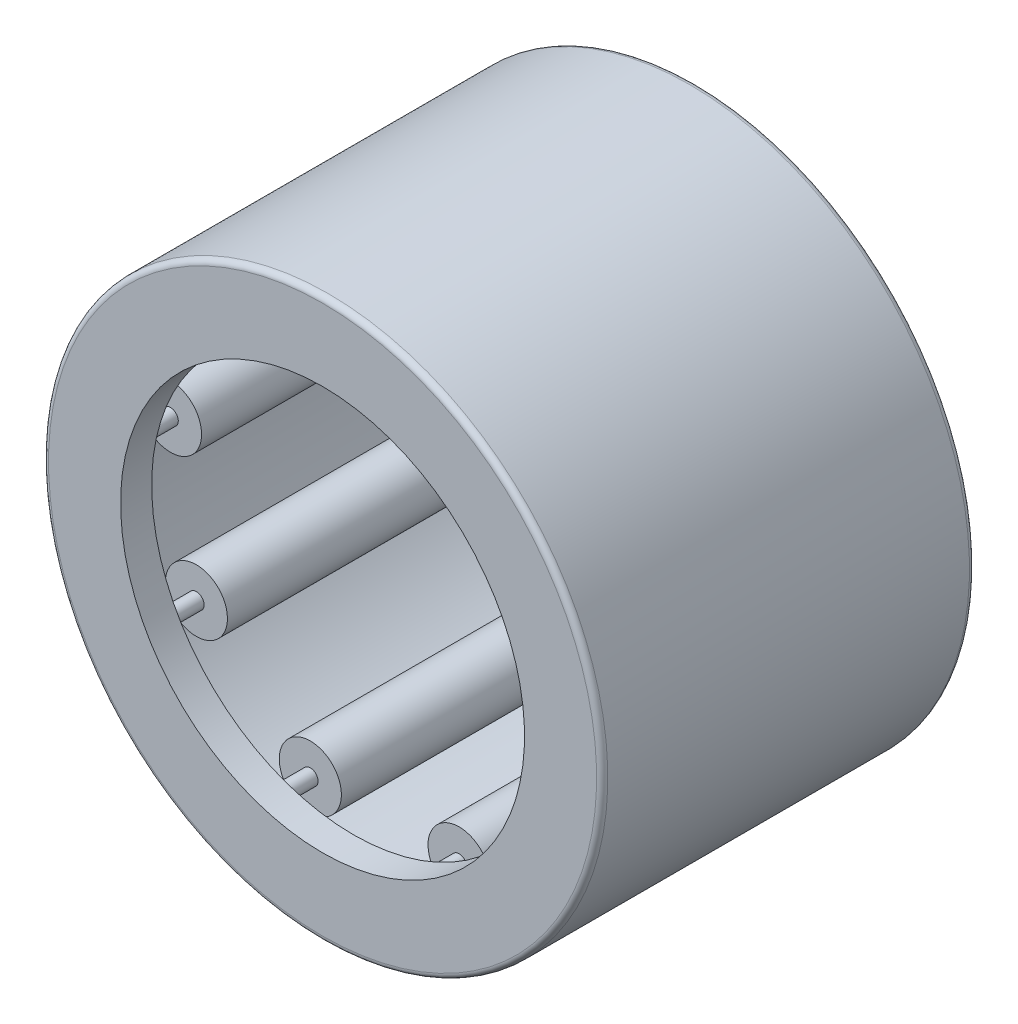
SolidWorks part; units mm, degrees
ref_plane "Front Plane" through (0, 0, 0) normal (0, 0, 1) x (1, 0, 0)
ref_plane "Top Plane" through (0, 0, 0) normal (0, 1, 0) x (1, 0, 0)
ref_plane "Right Plane" through (0, 0, 0) normal (1, 0, 0) x (0, 0, -1)
sketch "Sketch1" plane through (0, 0, 0) normal (1, 0, 0) x (0, 0, -1)
  line L0 (-4, 0) -> (4, 0) construction
  line L1 (0, 0) -> (0, 6) construction
  line L2 (-4, 0) -> (-4, 6) construction
  line L3 (-4, 6) -> (4, 6)
  line L4 (4, 6) -> (4, 0) construction
  line L5 (4, 0) -> (3.3333, 0) construction
  line L6 (3.3333, 0) -> (3.3333, 5.3333) construction
  line L7 (3.3333, 5.3333) -> (-3.3333, 5.3333)
  line L8 (-3.3333, 5.3333) -> (-3.3333, 0) construction
  line L9 (-3.3333, 0) -> (-4, 0) construction
  line L10 (-4, 6) -> (-4, 4.3333)
  line L11 (-4, 4.3333) -> (-3.3333, 4.3333)
  line L12 (-3.3333, 4.3333) -> (-3.3333, 5.3333)
  line L13 (3.3333, 6) -> (3.3333, 5.3333) construction
  line L14 (3.3333, 5.3333) -> (3.3333, 4.3333)
  line L15 (3.3333, 4.3333) -> (4, 4.3333)
  line L16 (4, 4.3333) -> (4, 6)
  line L17 (3.3333, 5.3333) -> (3.3333, 4.6667) construction
  line L18 (3.3333, 4.6667) -> (3.3333, 4) construction
  line L19 (3.3333, -5.3333) -> (3.3333, -4.6667) construction
  line L20 (3.3333, -6) -> (3.3333, -5.3333) construction
  line L21 (4, -4.3333) -> (4, -6) construction
  line L22 (3.3333, -4.3333) -> (4, -4.3333) construction
  line L23 (3.3333, -5.3333) -> (3.3333, -4.3333) construction
  line L24 (-3.3333, -4.3333) -> (-3.3333, -5.3333) construction
  line L25 (-4, -4.3333) -> (-3.3333, -4.3333) construction
  line L26 (-4, -6) -> (-4, -4.3333) construction
  line L27 (3.3333, -5.3333) -> (-3.3333, -5.3333) construction
  line L28 (-4, -6) -> (4, -6) construction
  point P5 (0, 4)
  dimension "Width" = 8
  dimension "OD" = 12
  dimension "Shaft Dia" = 8
revolve "Revolve1" add sketch "Sketch1" angle 360 about L0
sketch "Sketch2" plane through (0, 0, 0) normal (1, 0, 0) x (0, 0, -1)
  line L0 (3.3333, 5.3333) -> (-3.3333, 5.3333) construction
  line L1 (-2.6667, 4.6667) -> (2.6667, 4.6667) construction
  line L2 (-2.6667, 4.6667) -> (-2.6667, 5.3333) construction
  line L3 (-2.6667, 5.3333) -> (2.6667, 5.3333)
  line L4 (2.6667, 4.6667) -> (2.6667, 5.3333) construction
  line L5 (3.3333, 4.3333) -> (4, 4.3333) construction
  line L6 (-3.3333, 4.6667) -> (-2.6667, 4.6667) construction
  line L7 (2.6667, 4.6667) -> (3.3333, 4.6667) construction
  line L8 (-4, 4.3333) -> (-3.3333, 4.3333) construction
  line L9 (-2.6667, 4.8333) -> (-2.6667, 4.5) construction
  line L10 (-3.3333, 4.6667) -> (-3.3333, 4.3333) construction
  line L11 (-2.6667, 5.3333) -> (-2.6667, 4.8333)
  line L12 (2.6667, 5.3333) -> (2.6667, 4.8333)
  line L13 (2.6667, 4.8333) -> (-2.6667, 4.8333)
  line L14 (0, 5.3333) -> (0, 4) construction
  line L15 (-3.3333, 4.3333) -> (-3.3333, 5.3333) construction
  line L16 (-2.6667, 4.5) -> (-3.3333, 4.5) construction
  line L17 (0, 0) -> (4, 0) construction
  line L18 (-2.6667, -4.5) -> (-3.3333, -4.5) construction
  line L19 (0, -5.3333) -> (0, -4) construction
  line L20 (-3.3333, -4.6667) -> (-3.3333, -4.3333) construction
  line L21 (-2.6667, -4.8333) -> (-2.6667, -4.5) construction
  line L22 (2.6667, -4.6667) -> (3.3333, -4.6667) construction
  line L23 (-3.3333, -4.6667) -> (-2.6667, -4.6667) construction
  line L24 (2.6667, -4.6667) -> (2.6667, -5.3333) construction
  line L25 (-2.6667, -4.6667) -> (-2.6667, -5.3333) construction
  line L26 (-2.6667, -4.6667) -> (2.6667, -4.6667) construction
  line L27 (2.6667, -4.8333) -> (-2.6667, -4.8333) construction
  line L28 (2.6667, -5.3333) -> (2.6667, -4.8333) construction
  line L29 (-2.6667, -5.3333) -> (-2.6667, -4.8333) construction
  line L30 (-2.6667, -5.3333) -> (2.6667, -5.3333) construction
  line L31 (4, -6) -> (4, 6) construction
  line L32 (3.3333, 5.3333) -> (3.3333, 4.3333) construction
  point P16 (0, 4.6667)
revolve "Revolve2" add sketch "Sketch2" angle 360 about L1
sketch "Sketch3" plane through (0, 0, 0) normal (1, 0, 0) x (0, 0, -1)
  line L0 (3.3333, 5.3333) -> (3.3333, 4.3333) construction
  line L1 (-3.3333, 4.6667) -> (3.3333, 4.6667)
  line L2 (-3.3333, 4.6667) -> (-3.3333, 4.8333)
  line L3 (-3.3333, 4.8333) -> (3.3333, 4.8333)
  line L4 (3.3333, 4.6667) -> (3.3333, 4.8333)
  line L5 (0, 0) -> (4, 0) construction
  line L6 (4, -6) -> (4, 6) construction
  line L7 (3.3333, -4.6667) -> (3.3333, -4.8333) construction
  line L8 (-3.3333, -4.8333) -> (3.3333, -4.8333) construction
  line L9 (-3.3333, -4.6667) -> (-3.3333, -4.8333) construction
  line L10 (-3.3333, -4.6667) -> (3.3333, -4.6667) construction
revolve "Revolve3" add sketch "Sketch3" angle 360 about L1
ref_axis "Axis1" through (0, 0, -4) along (0, 0, 1)
pattern_circular "CirPattern1" count 9 every 40 about axis through (0, 0, -4) along (0, 0, 1) of bodies 166 167
fillet "Fillet1" radius 0.12 2 edges at (0, -6, -4) (0, -6, 4)
sketch "Sketch4" plane through (0, 0, 0) normal (1, 0, 0) x (0, 0, -1)
  line L0 (2.6667, 5.3333) -> (2.6667, 4.8333) construction
  line L1 (3.88, 4) -> (2.6667, 4)
  line L2 (3.88, 4) -> (3.88, 4.3333)
  line L3 (3.88, 4.3333) -> (2.6667, 4.3333)
  line L4 (2.6667, 4) -> (2.6667, 4.3333)
  line L5 (-4, 4.3333) -> (-3.3333, 4.3333) construction
  line L6 (3.88, -6) -> (3.88, 6) construction
revolve "Revolve4" [suppressed] add sketch "Sketch4" angle 360 about L0
sketch "Sketch5" plane through (0, 0, 0) normal (1, 0, 0) x (0, 0, -1)
  line L0 (-3.88, 6) -> (-3.88, -6) construction
  line L1 (-2.6667, 4) -> (-3.88, 4)
  line L2 (-2.6667, 4) -> (-2.6667, 4.3333)
  line L3 (-2.6667, 4.3333) -> (-3.88, 4.3333)
  line L4 (-3.88, 4) -> (-3.88, 4.3333)
  line L5 (-2.6667, 5.3333) -> (-2.6667, 4.8333) construction
revolve "Revolve5" [suppressed] add sketch "Sketch5" angle 360 about L0
equation "\"Angle@CirPattern1\" = 360/\"Rollers@CirPattern1\""
equation "\"Rollers@CirPattern1\" = \"OD@Sketch1\"*.75"
equation "\"D1@Fillet1\" = \"OD@Sketch1\"*.01"
